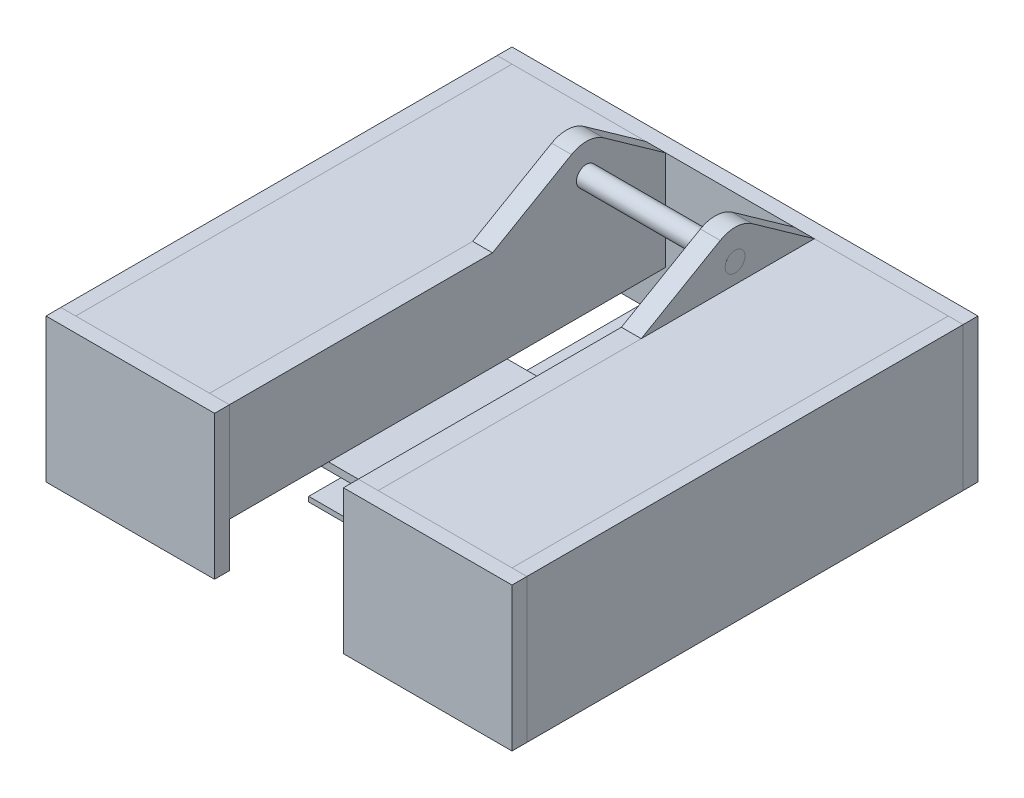
SolidWorks part; units mm, degrees
material "Alum Plate"
ref_plane "Front Plane" through (0, 0, 0) normal (0, 0, 1) x (1, 0, 0)
ref_plane "Top Plane" through (0, 0, 0) normal (0, 1, 0) x (1, 0, 0)
ref_plane "Right Plane" through (0, 0, 0) normal (1, 0, 0) x (0, 0, -1)
other "Bounding Box"
ref_plane "Default Plane" through (-8.9266, -12.7485, 0) normal (-0.1736, 0.9848, 0) x (0.9848, 0.1736, 0)
sketch "Sketch1" plane through (0, 0, 0) normal (0, 1, 0) x (1, 0, 0)
  line L0 (-139.7, 101.6) -> (-101.6, 101.6) construction
  line L1 (-139.7, -139.7) -> (139.7, -139.7)
  line L2 (-139.7, -139.7) -> (-139.7, 139.7)
  line L3 (-139.7, 139.7) -> (139.7, 139.7)
  line L4 (139.7, -139.7) -> (139.7, 139.7)
  line L5 (-139.7, -139.7) -> (139.7, 139.7) construction
  line L6 (-139.7, 139.7) -> (139.7, -139.7) construction
  line L7 (-101.6, 101.6) -> (-101.6, 139.7) construction
  line L8 (-41.275, -149.225) -> (-41.275, 149.225)
  line L9 (149.225, -149.225) -> (-149.225, -149.225)
  line L10 (149.225, -149.225) -> (149.225, 149.225)
  line L11 (149.225, 149.225) -> (-149.225, 149.225)
  line L12 (-149.225, -149.225) -> (-149.225, 149.225)
  line L13 (149.225, -149.225) -> (-149.225, 149.225) construction
  line L14 (149.225, 149.225) -> (-149.225, -149.225) construction
  line L15 (41.275, -149.225) -> (41.275, 149.225)
  line L16 (-41.275, 0) -> (0, 0) construction
  line L17 (0, 0) -> (41.275, 0) construction
  line L18 (-101.6, 101.6) -> (-82.55, 50.8)
  line L19 (-82.55, 50.8) -> (-120.65, 50.8)
  line L20 (-101.6, 101.6) -> (-101.6, 50.8) construction
  line L21 (-53.975, -149.225) -> (-53.975, 149.225)
  line L22 (53.975, -149.225) -> (53.975, 149.225)
  line L23 (-53.975, 0) -> (-41.275, 0) construction
  line L24 (41.275, 0) -> (53.975, 0) construction
  line L25 (-63.5, 29.845) -> (-63.5, 139.7) construction
  line L30 (-63.5, 84.7725) -> (-101.6, 84.7725) construction
  line L31 (-101.6, 84.7725) -> (-139.7, 84.7725) construction
  line L38 (-139.7, 29.845) -> (139.7, 29.845) construction
  line L39 (-139.7, -29.845) -> (139.7, -29.845) construction
  line L40 (0, -29.845) -> (0, 0) construction
  line L41 (0, 0) -> (0, 29.845) construction
  circle A0 centre (-101.6, 101.6) radius 32.5
  circle A1 centre (-82.55, 50.8) radius 18
  circle A2 centre (-120.65, 50.8) radius 14
  point P0 (0, 0)
  point P9 (0, 0)
  dimension "D3" = 65
  dimension "D6" = 36
  dimension "D7" = 28
  dimension "D1" = 9.525
  dimension "D2" = 38.1
  dimension "D4" = 279.4
  dimension "D5" = 82.55
  dimension "D8" = 38.1
  dimension "D9" = 50.8
  dimension "D10" = 12.7
  dimension "D11" = 9.525
  dimension "D15" = 20.955
sketch "Sketch2" plane through (0, 0, 0) normal (1, 0, 0) x (0, 0, -1)
  line L0 (0, 0) -> (234.4341, 0) construction
  line L2 (101.6, 25.4) -> (101.6, 92.075) construction
  line L3 (101.6, 50.8) -> (101.6, 53.975)
  line L4 (69.1, 53.975) -> (134.1, 53.975)
  line L5 (69.1, 53.975) -> (69.1, 60.975)
  line L6 (69.1, 60.975) -> (134.1, 60.975)
  line L7 (134.1, 53.975) -> (134.1, 60.975)
  line L8 (69.1, 53.975) -> (134.1, 60.975) construction
  line L9 (69.1, 60.975) -> (134.1, 53.975) construction
  line L10 (69.1, 85.075) -> (134.1, 85.075)
  line L11 (69.1, 85.075) -> (69.1, 92.075)
  line L12 (69.1, 92.075) -> (134.1, 92.075)
  line L13 (134.1, 85.075) -> (134.1, 92.075)
  line L14 (69.1, 85.075) -> (134.1, 92.075) construction
  line L15 (69.1, 92.075) -> (134.1, 85.075) construction
  line L16 (69.1, 60.975) -> (69.1, 73.025)
  line L17 (-139.7, 53.975) -> (139.7, 53.975)
  line L18 (-139.7, 53.975) -> (-139.7, 60.325)
  line L19 (-139.7, 60.325) -> (139.7, 60.325)
  line L20 (139.7, 53.975) -> (139.7, 60.325)
  line L21 (139.7, 85.725) -> (-139.7, 85.725)
  line L22 (139.7, 85.725) -> (139.7, 92.075)
  line L23 (139.7, 92.075) -> (-139.7, 92.075)
  line L24 (-139.7, 85.725) -> (-139.7, 92.075)
  line L33 (149.225, 12.7) -> (139.7, 12.7)
  line L34 (149.225, 12.7) -> (149.225, 104.775)
  line L35 (149.225, 104.775) -> (139.7, 104.775)
  line L36 (139.7, 12.7) -> (139.7, 104.775)
  line L37 (-149.225, 12.7) -> (-139.7, 12.7)
  line L38 (-149.225, 12.7) -> (-149.225, 104.775)
  line L39 (-149.225, 104.775) -> (-139.7, 104.775)
  line L40 (-139.7, 12.7) -> (-139.7, 104.775)
  line L41 (69.1, 73.025) -> (69.1, 85.075)
  line L42 (-139.7, 101.6) -> (139.7, 101.6)
  line L43 (-139.7, 101.6) -> (-139.7, 104.775)
  line L44 (-139.7, 104.775) -> (139.7, 104.775)
  line L45 (139.7, 101.6) -> (139.7, 104.775)
  circle A0 centre (101.6, 25.4) radius 25.4
  point P3 (101.6, 57.475)
  point P11 (101.6, 88.575)
  point P37 (69.1, 73.025)
  dimension "D1" = 50.8
  dimension "D2" = 7
  dimension "D3" = 65
  dimension "D4" = 3.175
  dimension "D5" = 38.1
  dimension "D6" = 6.35
  dimension "D7" = 12.7
  dimension "D9" = 12.7
  dimension "D10" = 3.175
ref_plane "Plane1" through (0, 53.975, 0) normal (0, 1, 0) x (1, 0, 0)
sketch "Sketch3" plane through (0, 53.975, 0) normal (0, 1, 0) x (1, 0, 0)
  line L0 (-53.975, -149.225) -> (-53.975, 149.225) construction
  line L1 (-139.7, 139.7) -> (-53.975, 139.7)
  line L2 (-139.7, 139.7) -> (-139.7, 29.845)
  line L3 (-139.7, 29.845) -> (-53.975, 29.845)
  line L4 (-53.975, 139.7) -> (-53.975, 29.845)
  line L5 (-139.7, 29.845) -> (139.7, 29.845) construction
  circle A0 centre (-101.6, 101.6) radius 32.5 construction
  circle A1 centre (-101.6, 101.6) radius 32.5
extrude "Boss-Extrude1" add sketch "Sketch3" along normal up to vertex (6.35 mm away) up to point (0, 60.325, -139.7)
ref_plane "Plane2" through (0, 73.025, 0) normal (0, 1, 0) x (1, 0, 0)
mirror "Mirror1" about plane through (0, 73.025, 0) normal (0, 1, 0) of bodies 104
mirror "Mirror2" about plane through (0, 0, 0) normal (0, 0, 1) of bodies 104 105
sketch "Sketch4" plane through (0, 0, 0) normal (1, 0, 0) x (0, 0, -1)
  line L0 (88.9, 117.475) -> (-12.7, 82.55)
  line L1 (-12.7, 82.55) -> (-152.4, 82.55)
  line L2 (-152.4, 6.35) -> (-152.4, 0) construction
  line L3 (149.225, 0) -> (-149.225, 0) construction
  line L4 (139.7, 12.7) -> (139.7, 104.775) construction
  line L5 (-200000, 0) -> (200234.4341, 0) construction
  line L6 (3.0575, 76.2) -> (88.9, 117.475)
  line L7 (72.8459, 44.45) -> (116.84, 69.85)
  line L8 (116.84, 69.85) -> (88.9, 117.475)
  line L9 (139.7, 92.075) -> (-139.7, 92.075) construction
  line L10 (-12.7, 82.55) -> (-12.7, 117.475) construction
  line L11 (-12.7, 117.475) -> (88.9, 117.475) construction
  line L12 (72.8459, 19.5453) -> (116.84, 48.85) construction
  line L13 (-139.7, 101.6) -> (139.7, 101.6) construction
  circle A0 centre (88.9, 117.475) radius 6.35
  circle A1 centre (-152.4, 82.55) radius 76.2
  circle A2 centre (72.8459, 44.45) radius 24.9047
  circle A3 centre (116.84, 69.85) radius 21
  circle A6 centre (3.0575, 76.2) radius 18
  point P17 (44.6726, 113.0319)
  point P20 (116.84, 71.6309)
  point P24 (27.0849, 72.918)
  point P25 (0, 69.85)
  dimension "D1" = 12.7
  dimension "D2" = 152.4
  dimension "D7" = 49.8094
  dimension "D8" = 42
  dimension "D10" = 36
  dimension "D3" = 6.35
  dimension "D4" = 50.8
  dimension "D5" = 117.475
  dimension "D6" = 139.7
  dimension "D9" = 241.3
  dimension "D11" = 22.86
  dimension "D12" = 95.25
  dimension "D13" = 22.225
  dimension "D14" = 44.45
  dimension "D15" = 50.8
  dimension "D16" = 25.4
sketch "Sketch6" plane through (0, 0, 0) normal (0, 1, 0) x (1, 0, 0)
  line L1 (-23.0411, 101.6113) -> (38.1, 101.6113)
  line L2 (-23.0411, 101.6113) -> (-23.0411, 76.0653)
  line L3 (-23.0411, 76.0653) -> (38.1, 76.0653)
  line L4 (38.1, 101.6113) -> (38.1, 76.0653)
  line L5 (-23.0411, 101.6113) -> (38.1, 76.0653) construction
  line L6 (-23.0411, 76.0653) -> (38.1, 101.6113) construction
  line L8 (-29.573, 133.8479) -> (17.8695, 133.8479)
  line L9 (-29.573, 133.8479) -> (-29.573, 110.7349)
  line L10 (-29.573, 110.7349) -> (17.8695, 110.7349)
  line L11 (17.8695, 133.8479) -> (17.8695, 110.7349)
  line L12 (-29.573, 133.8479) -> (17.8695, 110.7349) construction
  line L13 (-29.573, 110.7349) -> (17.8695, 133.8479) construction
  point P0 (7.5295, 88.8383)
  point P5 (-5.8518, 122.2914)
sketch "Sketch7" plane through (-53.975, 0, 0) normal (1, 0, 0) x (0, 0, -1)
  line L0 (99.9272, 133.0089) -> (139.7, 104.775)
  line L1 (139.7, 104.775) -> (139.7, 41.275)
  line L2 (139.7, 41.275) -> (-139.7, 41.275)
  line L3 (-139.7, 41.275) -> (-139.7, 104.775)
  line L4 (-139.7, 104.775) -> (28.803, 104.775)
  line L6 (28.803, 104.775) -> (79.375, 133.9728)
  line L7 (-139.7, 53.975) -> (139.7, 53.975) construction
  circle A0 centre (88.9, 117.475) radius 6.35 construction
  circle A1 centre (88.9, 117.475) radius 6.35
  arc A2 (79.375, 133.9728) -> (99.9272, 133.0089) centre (88.9, 117.475) cw
  dimension "D1" = 19.05
  dimension "D2" = 12.7
  dimension "D3" = 30
extrude "Boss-Extrude2" add sketch "Sketch7" along normal up to vertex (12.7 mm away) separate body up to point (-41.275, 0, -149.225)
sketch "Sketch8" plane through (0, 0, 139.7) normal (0, 0, 1) x (1, 0, 0)
  line L0 (-41.275, 104.775) -> (-41.275, 41.275) construction
  line L1 (-41.275, 12.7) -> (-149.225, 12.7)
  line L2 (-41.275, 12.7) -> (-41.275, 104.775)
  line L3 (-41.275, 104.775) -> (-149.225, 104.775)
  line L4 (-149.225, 12.7) -> (-149.225, 104.775)
extrude "Boss-Extrude3" add sketch "Sketch8" along normal up to vertex (9.525 mm away) separate body up to point (-149.225, 0, 149.225)
sketch "Sketch10" plane through (-139.7, 0, 0) normal (-1, 0, 0) x (0, 0, 1)
  line L0 (-139.7, 12.7) -> (-139.7, 104.775) construction
  line L1 (139.7, 104.775) -> (-139.7, 104.775)
  line L2 (139.7, 104.775) -> (139.7, 12.7)
  line L3 (139.7, 12.7) -> (-139.7, 12.7)
  line L4 (-139.7, 104.775) -> (-139.7, 12.7)
extrude "Boss-Extrude4" add sketch "Sketch10" along normal up to vertex (9.525 mm away) separate body up to point (-149.225, 0, -149.225)
sketch "Sketch13" plane through (0, 104.775, 0) normal (0, 1, 0) x (1, 0, 0)
  line L1 (-139.7, 139.7) -> (-53.975, 139.7)
  line L2 (-139.7, 139.7) -> (-139.7, -139.7)
  line L3 (-139.7, -139.7) -> (-53.975, -139.7)
  line L4 (-53.975, 139.7) -> (-53.975, -139.7)
extrude "Boss-Extrude7" add sketch "Sketch13" against normal up to vertex (3.175 mm away) separate body up to point (0, 101.6, 139.7)
mirror "Mirror3" about plane through (0, 0, 0) normal (1, 0, 0) of bodies 106 107 104 105 112 115 114 120
sketch "Sketch11" plane through (0, 0, -139.7) normal (0, 0, -1) x (-1, 0, 0)
  line L0 (-149.225, 104.775) -> (149.225, 104.775)
  line L1 (149.225, 104.775) -> (149.225, 12.7)
  line L2 (149.225, 12.7) -> (-149.225, 12.7)
  line L3 (-149.225, 12.7) -> (-149.225, 104.775)
  line L4 (0, 104.775) -> (0, 0) construction
  line L5 (149.225, 104.775) -> (149.225, 12.7) construction
extrude "Boss-Extrude5" add sketch "Sketch11" along normal up to vertex (9.525 mm away) separate body up to point (-149.225, 0, -149.225)
sketch "Sketch12" plane through (0, 41.275, 0) normal (0, -1, 0) x (1, 0, 0)
  line L0 (53.975, 139.7) -> (53.975, -139.7) construction
  line L1 (-53.975, 76.2) -> (53.975, 76.2)
  line L2 (-53.975, 76.2) -> (-53.975, -38.1)
  line L3 (-53.975, -38.1) -> (53.975, -38.1)
  line L4 (53.975, 76.2) -> (53.975, -38.1)
  line L5 (-139.7, -139.7) -> (139.7, -139.7) construction
  line L6 (53.975, 149.225) -> (53.975, -149.225) construction
  line L7 (-53.975, 149.225) -> (-53.975, -149.225) construction
  line L8 (-139.7, 139.7) -> (139.7, 139.7) construction
  dimension "D1" = 101.6
  dimension "D2" = 63.5
extrude "Boss-Extrude6" add sketch "Sketch12" along normal blind 4.7625 separate body
sketch "Sketch14" plane through (0, 12.7, 0) normal (0, -1, 0) x (1, 0, 0)
  line L0 (-139.7, 33.02) -> (-53.975, 33.02)
  line L1 (-139.7, 139.7) -> (-139.7, -139.7) construction
  line L2 (-53.975, 149.225) -> (-53.975, -149.225) construction
  line L3 (-53.975, 33.02) -> (-53.975, 76.2)
  line L4 (-53.975, 76.2) -> (53.975, 76.2)
  line L5 (53.975, 76.2) -> (53.975, 33.02)
  line L6 (53.975, 149.225) -> (53.975, -149.225) construction
  line L7 (53.975, 33.02) -> (139.7, 33.02)
  line L8 (139.7, 139.7) -> (139.7, -139.7) construction
  line L9 (139.7, 33.02) -> (139.7, -33.02)
  line L10 (139.7, -33.02) -> (53.975, -33.02)
  line L11 (53.975, -33.02) -> (53.975, -139.7)
  line L12 (53.975, -139.7) -> (-53.975, -139.7)
  line L14 (-53.975, -139.7) -> (-53.975, -33.02)
  line L15 (-53.975, -33.02) -> (-139.7, -33.02)
  line L16 (-139.7, -33.02) -> (-139.7, 33.02)
  line L17 (-139.7, 29.845) -> (139.7, 29.845) construction
  line L18 (-96.8375, -33.02) -> (-96.8375, -29.845) construction
  line L19 (-139.7, -29.845) -> (139.7, -29.845) construction
  line L20 (-96.8375, 33.02) -> (-96.8375, 29.845) construction
  line L21 (-139.7, -139.7) -> (139.7, -139.7) construction
  dimension "D1" = 3.175
extrude "Boss-Extrude8" add sketch "Sketch14" against normal blind 3.175 separate body
sketch "Sketch15" plane through (-53.975, 0, 0) normal (-1, 0, 0) x (0, 0, 1)
  circle A0 centre (-88.9, 117.475) radius 6.35 construction
  circle A1 centre (-88.9, 117.475) radius 6.35
extrude "Boss-Extrude9" add sketch "Sketch15" against normal up to surface (107.95 mm away) separate body up to face at (53.975, 95.2671, -29.7495)
